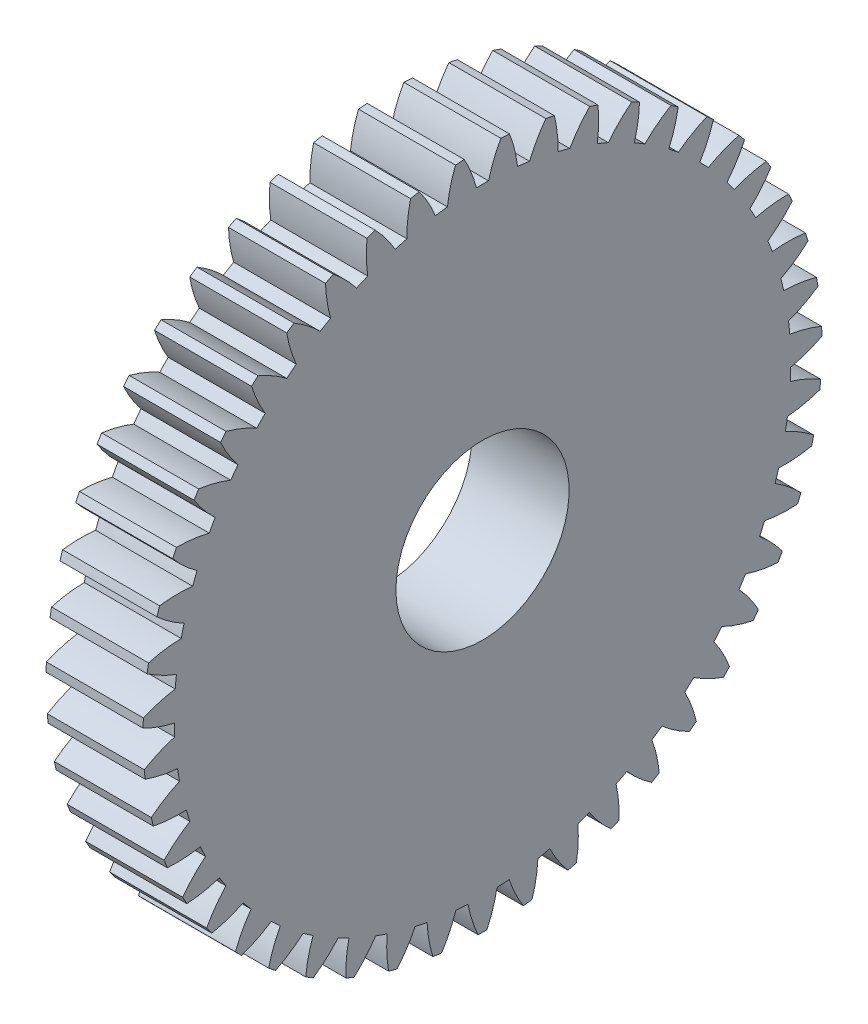
SolidWorks part; units mm, degrees
ref_plane "Plane1" through (0, 0, 0) normal (0, 0, 1) x (1, 0, 0)
ref_plane "Plane2" through (0, 0, 0) normal (0, 1, 0) x (1, 0, 0)
ref_plane "Plane3" through (0, 0, 0) normal (1, 0, 0) x (0, 0, -1)
sketch "HoldingSke" plane through (0, 0, 0) normal (0, 1, 0) x (1, 0, 0)
  line L0 (0, 0) -> (1.705, -1.8284)
  line L1 (-15, 0) -> (100, 0) construction
  line L2 (0, 0) -> (-2.1039, 2.3779)
  line L3 (0, 0) -> (-11.863, 4.5341)
  line L4 (0, 0) -> (5.8897, 6.316)
  line L5 (0, 0) -> (-46.8476, -17.4728)
  line L6 (0, 0) -> (-2.3211, -1.5661)
  line L7 (-2.1039, 2.3779) -> (8.6586, 51.2059)
  line L8 (-76.2, 54.61) -> (-75.3, 54.61)
  line L9 (-71.009, 38.7566) -> (-53.1078, 45.2721)
  line L10 (-76.2, 71.12) -> (104.1128, 71.12)
  line L11 (0, 0) -> (-2.8, 0)
  line L12 (-76.2, 101.6) -> (-76.185, 101.6)
  line L13 (24.9733, 27.94) -> (52.9518, 28.4284)
  line L14 (24.9733, 27.94) -> (24.9743, 27.94)
  line L15 (24.9733, 27.94) -> (100.4006, 29.5858)
  line L16 (-63.627, -0.4) -> (-12.827, -0.4)
  circle A0 centre (0, 0) radius 2.5
  circle A1 centre (0, 0) radius 8.899
  circle A2 centre (0, 0) radius 37.5
  circle A3 centre (0, 0) radius 2.5
  dimension "MHD" = 17.798
  dimension "Hub_dia" = 75
  dimension "Bore" = 5
  dimension "MBD" = 5
  dimension "Num_teeth" = 47
  dimension "Pitch" = 2.5
  dimension "Overall_len" = 50
  dimension "Show_teeth" = 47
  dimension "Thickness" = 2.8
  dimension "OAL" = 50.0001
  dimension "T_dim" = 0.9
  dimension "Ap" = 20
  dimension "H" = 19.05
  dimension "Pitch_radius" = 180.3128
  dimension "Width" = 2.8
  dimension "Backlash" = 0.015
  dimension "Addendum_fac" = 1
  dimension "Dedendum_fac" = 1.25
  dimension "Clearance_fac" = 0.25
  dimension "Dedendum_add" = 0.001
  dimension "Module" = 0.4
sketch "BasProSke" plane through (0, 0, 0) normal (0, 1, 0) x (1, 0, 0)
  line L0 (-10, 0) -> (60, 0) construction
  line L1 (0, 0) -> (0, 9.8)
  line L2 (0, 0) -> (2.8, 0)
  line L3 (2.8, 0) -> (2.8, 9.8)
  line L4 (2.8, 9.8) -> (0, 9.8)
  dimension "Thickness" = 2.8
  dimension "Diameter" = 19.6
revolve "Base-Revolve" add sketch "BasProSke" angle 360 about L0
sketch "TooCutSke" plane through (0, 0, 0) normal (1, 0, 0) x (0, 0, -1)
  line L1 (0, 0) -> (0, 107) construction
  line L2 (0, 0) -> (-0.3403, 9.3938) construction
  line L3 (0, 0) -> (-1.2551, 18.7492) construction
  line L4 (-0.3403, 9.3938) -> (-0.6276, 9.3746) construction
  arc A0 (0.1757, 8.8973) -> (-0.1757, 8.8973) centre (0, 0) ccw
  arc A1 (0.5423, 9.8104) -> (-0.5423, 9.8104) centre (0, 0) ccw
  circle A2 centre (0, 0) radius 9.4 construction
  circle A3 centre (0, 0) radius 8.8331 construction
  arc A4 (-0.1757, 8.8973) -> (-0.5423, 9.8104) centre (-3.8184, 7.9652) ccw
  arc A5 (0.5423, 9.8104) -> (0.1757, 8.8973) centre (3.8184, 7.9652) ccw
  dimension "Root_dia" = 17.798
  dimension "Overcut_dia" = 19.6508
  dimension "Pitch_dia" = 18.8
  dimension "Base_dia" = 17.6662
  dimension "Flank_rad" = 3.76
  dimension "Half_ang" = 3.83
  dimension "Half_CT" = 0.2879
extrude "ToothCut" cut sketch "TooCutSke" along normal through all
fillet "Breaks" [suppressed] radius 0.008
fillet "RootFillets" [suppressed] radius 0.101
pattern_circular "TeethCuts" count 47 every 7.66 about axis through (-10, 0, 0) along (1, 0, 0) of "ToothCut", "RootFillets", "Breaks"
sketch "HubNeaOneSke" plane through (0, 0, 0) normal (-1, 0, 0) x (0, 0, 1)
  circle A0 centre (0, 0) radius 8.899
  dimension "Diameter" = 17.798
extrude "HubNearOne" [suppressed] add sketch "HubNeaOneSke" along normal blind 47.2001
sketch "HubNeaBotSke" plane through (0, 0, 0) normal (-1, 0, 0) x (0, 0, 1)
  circle A0 centre (0, 0) radius 8.899
  dimension "Diameter" = 17.798
extrude "HubNearBoth" [suppressed] add sketch "HubNeaBotSke" along normal blind 23.6
ref_plane "FarPln" through (2.8, 0, 0) normal (1, 0, 0) x (0, 0, -1)
sketch "HubFarSke" plane through (2.8, 0, 0) normal (1, 0, 0) x (0, 0, -1)
  circle A0 centre (0, 0) radius 8.899
  dimension "Diameter" = 17.798
extrude "HubFar" [suppressed] add sketch "HubFarSke" along normal blind 23.6
sketch "BorSke" plane through (0, 0, 0) normal (1, 0, 0) x (0, 0, -1)
  circle A0 centre (0, 0) radius 2.5
  dimension "Diameter" = 5
extrude "Bore" cut sketch "BorSke" along normal mid plane 100.0001
sketch "KeySke" plane through (0, 0, 0) normal (1, 0, 0) x (0, 0, -1)
  line L0 (-1, 0) -> (-1, 3.4)
  line L1 (-1, 3.4) -> (1, 3.4)
  line L2 (1, 3.4) -> (1, 0)
  line L3 (0, 0) -> (0, 34) construction
  line L4 (-1, 0) -> (1, 0)
  dimension "Offset" = 3.4
  dimension "Width" = 2
extrude "Keyway" [suppressed] cut sketch "KeySke" along normal mid plane 100.0001
pattern_circular "Keyway2" [suppressed] count 2 every 90 about axis through (-10, 0, 0) along (1, 0, 0)
equation "' \"Module@HoldingSke\" = 6.35"
equation "' \"Num_teeth@HoldingSke\" = 12"
equation "' \"Ap@HoldingSke\" =  20"
equation "' \"Ap@HoldingSke\" = 20"
equation "' \"Width@HoldingSke\" = 0.5 * 25.4"
equation "' \"Hub_dia@HoldingSke\"= 1 * 25.4"
equation "' \"Hub_dia@HoldingSke\" = 1 * 25.4"
equation "' \"Overall_len@HoldingSke\" = 1.0 * 25.4"
equation "' \"Bore@HoldingSke\" = 0.75 * 25.4"
equation "' \"T_dim@HoldingSke\" = 0.1 * 25.4"
equation "' \"Width@KeySke\" = 0.25 * 25.4"
equation "' \"Show_teeth@HoldingSke\" = 13"
equation "' \"Backlash@HoldingSke\" = 0.009 * 25.4"
equation "' \"Addendum_fac@HoldingSke\" = 1.0"
equation "' \"Dedendum_fac@HoldingSke\" = 1.25"
equation "' \"Dedendum_add@HoldingSke\" = 0.00005 * 25.4"
equation "' \"Clearance_fac@HoldingSke\" = 0.25"
equation "\"Pitch@HoldingSke\" = 1 / \"Module@HoldingSke\""
equation "\"Overcut_dia@TooCutSke\" = (\"Num_teeth@HoldingSke\" + 2 * \"Addendum_fac@HoldingSke\") / \"Pitch@HoldingSke\" + 0.002 * 25.4"
equation "\"Pitch_dia@TooCutSke\" = \"Num_teeth@HoldingSke\" / \"Pitch@HoldingSke\""
equation "\"Base_dia@TooCutSke\" = \"Num_teeth@HoldingSke\" / \"Pitch@HoldingSke\" * cos((\"Ap@HoldingSke\"  * 3.14159265 / 180))"
equation "\"Root_dia@TooCutSke\" = (\"Num_teeth@HoldingSke\" + 2) / \"Pitch@HoldingSke\" - 2 * (\"Addendum_fac@HoldingSke\" + \"Dedendum_fac@HoldingSke\") / \"Pitch@HoldingSke\" - \"Dedendum_add@HoldingSke\" * 2"
equation "\"Half_ang@TooCutSke\" = 180 / \"Num_teeth@HoldingSke\""
equation "\"Half_CT@TooCutSke\" = \"Num_teeth@HoldingSke\" / \"Pitch@HoldingSke\" * sin((3.14159265 / 2 / \"Num_teeth@HoldingSke\")) / 2 - 7 * \"Backlash@HoldingSke\" / 4"
equation "\"Flank_rad@TooCutSke\" = \"Num_teeth@HoldingSke\" / \"Pitch@HoldingSke\" / 5"
equation "\"Radius@RootFillets\" = \"Clearance_fac@HoldingSke\" / \"Pitch@HoldingSke\" + \"Dedendum_add@HoldingSke\""
equation "\"Break_rad@Breaks\" = 0.02 / \"Pitch@HoldingSke\""
equation "\"Thickness@HoldingSke\" = \"Width@HoldingSke\""
equation "\"OAL@HoldingSke\" = \"Thickness@HoldingSke\""
equation "\"MHD@HoldingSke\" = (\"Num_teeth@HoldingSke\" + 2) / \"Pitch@HoldingSke\" - 2 * (\"Addendum_fac@HoldingSke\" + \"Dedendum_fac@HoldingSke\")  / \"Pitch@HoldingSke\" - \"Dedendum_add@HoldingSke\" * 2"
equation "\"MBD@HoldingSke\" = (\"Num_teeth@HoldingSke\" + 2) / \"Pitch@HoldingSke\" - 2 * (\"Addendum_fac@HoldingSke\" + \"Dedendum_fac@HoldingSke\")  / \"Pitch@HoldingSke\" - \"Dedendum_add@HoldingSke\" * 2 - 0.002 * 25.4"
equation "\"MHD@HoldingSke\" = ((sgn( \"MHD@HoldingSke\" - \"Hub_dia@HoldingSke\" )-1)*( \"MHD@HoldingSke\" - \"Hub_dia@HoldingSke\" ))/-2+ \"Hub_dia@HoldingSke\""
equation "\"MBD@HoldingSke\" = ((sgn( \"MBD@HoldingSke\" - \"Bore@HoldingSke\" )-1)*( \"MBD@HoldingSke\" - \"Bore@HoldingSke\" ))/-2+ \"Bore@HoldingSke\""
equation "\"OAL@HoldingSke\" = ((sgn( \"OAL@HoldingSke\" - \"Overall_len@HoldingSke\" )+1)*( \"OAL@HoldingSke\" - \"Overall_len@HoldingSke\" ))/2 + \"Overall_len@HoldingSke\" + 0.000002 * 25.4"
equation "\"Num_teeth@TeethCuts\" = int( \"Show_teeth@HoldingSke\" ) + 1"
equation "\"Num_teeth@TeethCuts\" = ((sgn( \"Num_teeth@TeethCuts\" - \"Num_teeth@HoldingSke\" )-1)*( \"Num_teeth@TeethCuts\" - \"Num_teeth@HoldingSke\" ))/-2+ \"Num_teeth@HoldingSke\""
equation "\"Num_teeth@TeethCuts\" = ((sgn( \"Num_teeth@TeethCuts\" - 2.0)+1)*( \"Num_teeth@TeethCuts\" - 2.0))/2 +2.0"
equation "\"Angle@TeethCuts\" = 360.0 / \"Num_teeth@HoldingSke\""
equation "\"Diameter@BasProSke\" = (\"Num_teeth@HoldingSke\" + 2 * \"Addendum_fac@HoldingSke\") / \"Pitch@HoldingSke\""
equation "\"Thickness@BasProSke\"  = \"Thickness@HoldingSke\""
equation "' \"Fillet_rad@BasProSke\" =  \"Thickness@HoldingSke\" * 0.05"
equation "' \"Fillet_rad@BasProSke\" = \"Thickness@HoldingSke\" * 0.05"
equation "\"MHD@HoldingSke\" = ((sgn( \"MHD@HoldingSke\" - \"Root_dia@TooCutSke\" )-1)*( \"MHD@HoldingSke\" - \"Root_dia@TooCutSke\" ))/-2+ \"Root_dia@TooCutSke\""
equation "\"Diameter@HubNeaOneSke\" = \"MHD@HoldingSke\""
equation "\"Length@HubNearOne\" = \"OAL@HoldingSke\" - \"Thickness@BasProSke\""
equation "\"Diameter@HubNeaBotSke\" = \"MHD@HoldingSke\""
equation "\"Length@HubNearBoth\" = ( \"OAL@HoldingSke\" - \"Thickness@BasProSke\" ) / 2.0"
equation "\"Thickness@FarPln\" = \"Thickness@BasProSke\""
equation "\"Diameter@HubFarSke\" = \"MHD@HoldingSke\""
equation "\"Length@HubFar\" = ( \"OAL@HoldingSke\" - \"Thickness@BasProSke\" ) / 2.0"
equation "\"Diameter@BorSke\" = \"MBD@HoldingSke\""
equation "\"D1@Bore\" = \"OAL@HoldingSke\" * 2.0"
equation "\"D1@Keyway\" = \"OAL@HoldingSke\" * 2.0"
equation "\"Offset@KeySke\" = \"T_dim@HoldingSke\" + \"MBD@HoldingSke\" / 2.0"
